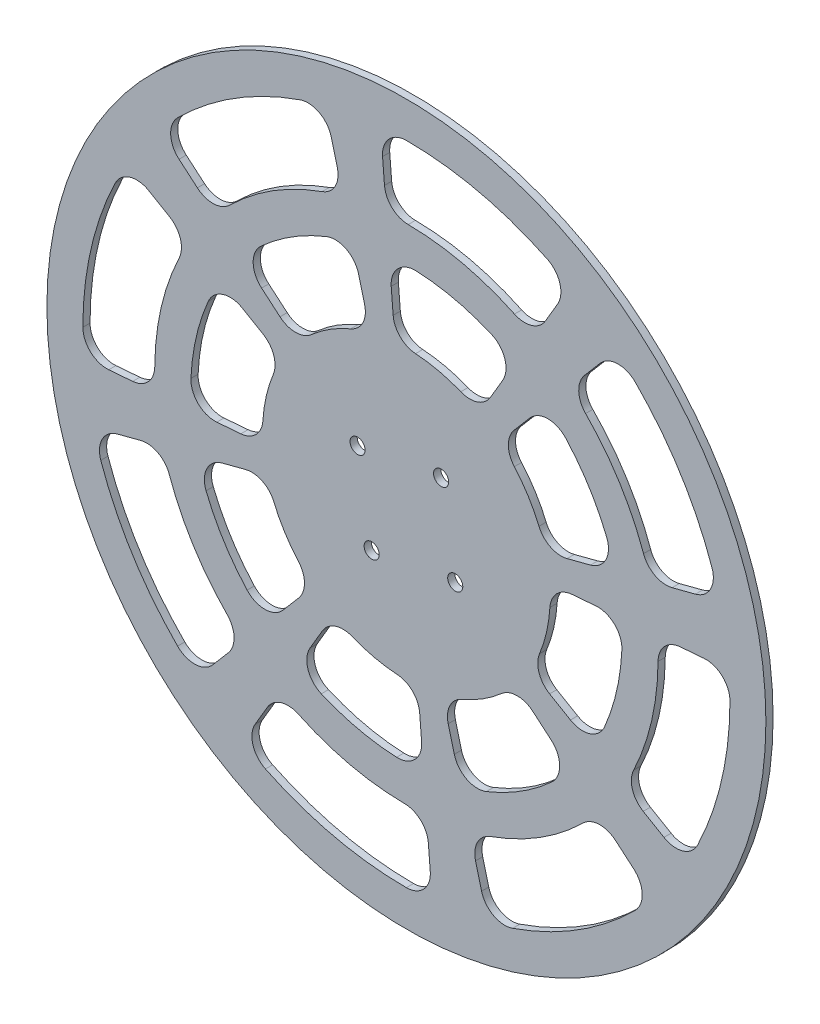
SolidWorks part; units mm, degrees
ref_plane "Front Plane" through (0, 0, 0) normal (0, 0, 1) x (1, 0, 0)
ref_plane "Top Plane" through (0, 0, 0) normal (0, 1, 0) x (1, 0, 0)
ref_plane "Right Plane" through (0, 0, 0) normal (1, 0, 0) x (0, 0, -1)
sketch "Sketch1" plane through (0, 0, 0) normal (0, 0, 1) x (1, 0, 0)
  line L0 (0, 0) -> (0, 140) construction
  line L1 (0, 140) -> (0, 150) construction
  line L2 (-12.5, 140) -> (12.5, 140) construction
  circle A0 centre (0, 0) radius 150
  circle A5 centre (20.3733, -14.4889) radius 3.15
  circle A6 centre (-14.4889, -20.3733) radius 3.15
  circle A7 centre (-20.3733, 14.4889) radius 3.15
  circle A8 centre (14.4889, 20.3733) radius 3.15
  point P9 (0, 140)
  point P21 (0, 0)
  dimension "D1" = 300
  dimension "D2" = 6.3
  dimension "D4" = 6.3
  dimension "D3" = 6.3
  dimension "D6" = 6.3
  dimension "D5" = 140
extrude "Boss-Extrude2" add sketch "Sketch1" along normal blind 3
sketch "Weight Reduction Cutouts" plane through (0, 0, 0) normal (0, 0, 1) x (1, 0, 0)
  line L3 (-33.985, 130.6523) -> (0, 0) construction
  line L4 (0, 0) -> (-102.778, 87.5311) construction
  line L5 (-94.8598, 80.7875) -> (-87.22, 74.2811)
  line L6 (-31.3667, 120.5866) -> (-28.8405, 110.8748)
  line L7 (-14.4889, -20.3733) -> (-20.3733, 14.4889) construction
  line L8 (-20.3733, 14.4889) -> (14.4889, 20.3733) construction
  line L9 (14.4889, 20.3733) -> (20.3733, -14.4889) construction
  line L10 (20.3733, -14.4889) -> (-14.4889, -20.3733) construction
  line L11 (-60.4278, 51.4634) -> (-52.7457, 44.921)
  line L12 (-19.9813, 76.8163) -> (-17.4411, 67.0508)
  line L13 (63.088, 107.4472) -> (58.007, 98.7937)
  line L14 (-9.9506, 124.2014) -> (-9.1492, 114.1985)
  line L15 (40.1884, 68.4463) -> (35.0793, 59.7448)
  line L16 (-6.3387, 79.119) -> (-5.5329, 69.0607)
  line L17 (120.5866, 31.3667) -> (110.8748, 28.8405)
  line L18 (80.7875, 94.8598) -> (74.2811, 87.22)
  line L19 (76.8163, 19.9813) -> (67.0508, 17.4411)
  line L20 (51.4634, 60.4278) -> (44.921, 52.7457)
  line L21 (107.4472, -63.088) -> (98.7937, -58.007)
  line L22 (124.2014, 9.9506) -> (114.1985, 9.1492)
  line L23 (68.4463, -40.1884) -> (59.7448, -35.0793)
  line L24 (79.119, 6.3387) -> (69.0607, 5.5329)
  line L25 (31.3667, -120.5866) -> (28.8405, -110.8748)
  line L26 (94.8598, -80.7875) -> (87.22, -74.2811)
  line L27 (19.9813, -76.8163) -> (17.4411, -67.0508)
  line L28 (60.4278, -51.4634) -> (52.7457, -44.921)
  line L29 (-63.088, -107.4472) -> (-58.007, -98.7937)
  line L30 (9.9506, -124.2014) -> (9.1492, -114.1985)
  line L31 (-40.1884, -68.4463) -> (-35.0793, -59.7448)
  line L32 (6.3387, -79.119) -> (5.5329, -69.0607)
  line L33 (-120.5866, -31.3667) -> (-110.8748, -28.8405)
  line L34 (-80.7875, -94.8598) -> (-74.2811, -87.22)
  line L35 (-76.8163, -19.9813) -> (-67.0508, -17.4411)
  line L36 (-51.4634, -60.4278) -> (-44.921, -52.7457)
  line L37 (-107.4472, 63.088) -> (-98.7937, 58.007)
  line L38 (-124.2014, -9.9506) -> (-114.1985, -9.1492)
  line L39 (-68.4463, 40.1884) -> (-59.7448, 35.0793)
  line L40 (-79.119, -6.3387) -> (-69.0607, -5.5329)
  line L41 (0, 0) -> (-25.6542, 151.9908) construction
  arc A6 (-95.4461, 95.4728) -> (-44.3283, 127.5147) centre (0, 0) cw
  arc A7 (-73.7156, 74.773) -> (-35.1691, 98.935) centre (0, 0) cw
  arc A8 (-60.687, 66.4612) -> (-33.3667, 83.5863) centre (0, 0) cw
  arc A9 (-39.6531, 45.0293) -> (-23.2449, 55.3143) centre (0, 0) cw
  arc A10 (-23.2449, 55.3143) -> (-17.4411, 67.0508) centre (-27.1191, 64.5334) ccw
  arc A11 (-39.6531, 45.0293) -> (-52.7457, 44.921) centre (-46.2619, 52.5342) cw
  arc A12 (-33.3667, 83.5863) -> (-19.9813, 76.8163) centre (-29.6593, 74.2989) cw
  arc A13 (-60.687, 66.4612) -> (-60.4278, 51.4634) centre (-53.944, 59.0766) ccw
  arc A14 (-35.1691, 98.935) -> (-28.8405, 110.8748) centre (-38.5185, 108.3574) ccw
  arc A15 (-73.7156, 74.773) -> (-87.22, 74.2811) centre (-80.7362, 81.8943) cw
  arc A16 (-44.3283, 127.5147) -> (-31.3667, 120.5866) centre (-41.0447, 118.0692) cw
  arc A17 (-95.4461, 95.4728) -> (-94.8598, 80.7875) centre (-88.376, 88.4007) ccw
  arc A18 (58.8217, 121.5113) -> (63.088, 107.4472) centre (54.4645, 112.5105) cw
  arc A19 (45.0893, 94.8259) -> (58.007, 98.7937) centre (49.3836, 103.8569) ccw
  arc A20 (0.7477, 104.9973) -> (45.0893, 94.8259) centre (0, 0) cw
  arc A21 (0.7477, 104.9973) -> (-9.1492, 114.1985) centre (0.8189, 114.9971) cw
  arc A22 (0.0189, 135) -> (-9.9506, 124.2014) centre (0.0175, 125) ccw
  arc A23 (0.0189, 135) -> (58.8217, 121.5113) centre (0, 0) cw
  arc A24 (35.5106, 82.6982) -> (40.1884, 68.4463) centre (31.565, 73.5095) cw
  arc A25 (22.6765, 55.5498) -> (35.0793, 59.7448) centre (26.4559, 64.8081) ccw
  arc A26 (3.8016, 59.8794) -> (22.6765, 55.5498) centre (0, 0) cw
  arc A27 (3.8016, 59.8794) -> (-5.5329, 69.0607) centre (4.4352, 69.8594) cw
  arc A28 (4.083, 89.9073) -> (-6.3387, 79.119) centre (3.6293, 79.9176) ccw
  arc A29 (4.083, 89.9073) -> (35.5106, 82.6982) centre (0, 0) cw
  arc A30 (127.5147, 44.3283) -> (120.5866, 31.3667) centre (118.0692, 41.0447) cw
  arc A31 (98.935, 35.1691) -> (110.8748, 28.8405) centre (108.3574, 38.5185) ccw
  arc A32 (74.773, 73.7156) -> (98.935, 35.1691) centre (0, 0) cw
  arc A33 (74.773, 73.7156) -> (74.2811, 87.22) centre (81.8943, 80.7362) cw
  arc A34 (95.4728, 95.4461) -> (80.7875, 94.8598) centre (88.4007, 88.376) ccw
  arc A35 (95.4728, 95.4461) -> (127.5147, 44.3283) centre (0, 0) cw
  arc A36 (83.5863, 33.3667) -> (76.8163, 19.9813) centre (74.2989, 29.6593) cw
  arc A37 (55.3143, 23.2449) -> (67.0508, 17.4411) centre (64.5334, 27.1191) ccw
  arc A38 (45.0293, 39.6531) -> (55.3143, 23.2449) centre (0, 0) cw
  arc A39 (45.0293, 39.6531) -> (44.921, 52.7457) centre (52.5342, 46.2619) cw
  arc A40 (66.4612, 60.687) -> (51.4634, 60.4278) centre (59.0766, 53.944) ccw
  arc A41 (66.4612, 60.687) -> (83.5863, 33.3667) centre (0, 0) cw
  arc A42 (121.5113, -58.8217) -> (107.4472, -63.088) centre (112.5105, -54.4645) cw
  arc A43 (94.8259, -45.0893) -> (98.7937, -58.007) centre (103.8569, -49.3836) ccw
  arc A44 (104.9973, -0.7477) -> (94.8259, -45.0893) centre (0, 0) cw
  arc A45 (104.9973, -0.7477) -> (114.1985, 9.1492) centre (114.9971, -0.8189) cw
  arc A46 (135, -0.0189) -> (124.2014, 9.9506) centre (125, -0.0175) ccw
  arc A47 (135, -0.0189) -> (121.5113, -58.8217) centre (0, 0) cw
  arc A48 (82.6982, -35.5106) -> (68.4463, -40.1884) centre (73.5095, -31.565) cw
  arc A49 (55.5498, -22.6765) -> (59.7448, -35.0793) centre (64.8081, -26.4559) ccw
  arc A50 (59.8794, -3.8016) -> (55.5498, -22.6765) centre (0, 0) cw
  arc A51 (59.8794, -3.8016) -> (69.0607, 5.5329) centre (69.8594, -4.4352) cw
  arc A52 (89.9073, -4.083) -> (79.119, 6.3387) centre (79.9176, -3.6293) ccw
  arc A53 (89.9073, -4.083) -> (82.6982, -35.5106) centre (0, 0) cw
  arc A54 (44.3283, -127.5147) -> (31.3667, -120.5866) centre (41.0447, -118.0692) cw
  arc A55 (35.1691, -98.935) -> (28.8405, -110.8748) centre (38.5185, -108.3574) ccw
  arc A56 (73.7156, -74.773) -> (35.1691, -98.935) centre (0, 0) cw
  arc A57 (73.7156, -74.773) -> (87.22, -74.2811) centre (80.7362, -81.8943) cw
  arc A58 (95.4461, -95.4728) -> (94.8598, -80.7875) centre (88.376, -88.4007) ccw
  arc A59 (95.4461, -95.4728) -> (44.3283, -127.5147) centre (0, 0) cw
  arc A60 (33.3667, -83.5863) -> (19.9813, -76.8163) centre (29.6593, -74.2989) cw
  arc A61 (23.2449, -55.3143) -> (17.4411, -67.0508) centre (27.1191, -64.5334) ccw
  arc A62 (39.6531, -45.0293) -> (23.2449, -55.3143) centre (0, 0) cw
  arc A63 (39.6531, -45.0293) -> (52.7457, -44.921) centre (46.2619, -52.5342) cw
  arc A64 (60.687, -66.4612) -> (60.4278, -51.4634) centre (53.944, -59.0766) ccw
  arc A65 (60.687, -66.4612) -> (33.3667, -83.5863) centre (0, 0) cw
  arc A66 (-58.8217, -121.5113) -> (-63.088, -107.4472) centre (-54.4645, -112.5105) cw
  arc A67 (-45.0893, -94.8259) -> (-58.007, -98.7937) centre (-49.3836, -103.8569) ccw
  arc A68 (-0.7477, -104.9973) -> (-45.0893, -94.8259) centre (0, 0) cw
  arc A69 (-0.7477, -104.9973) -> (9.1492, -114.1985) centre (-0.8189, -114.9971) cw
  arc A70 (-0.0189, -135) -> (9.9506, -124.2014) centre (-0.0175, -125) ccw
  arc A71 (-0.0189, -135) -> (-58.8217, -121.5113) centre (0, 0) cw
  arc A72 (-35.5106, -82.6982) -> (-40.1884, -68.4463) centre (-31.565, -73.5095) cw
  arc A73 (-22.6765, -55.5498) -> (-35.0793, -59.7448) centre (-26.4559, -64.8081) ccw
  arc A74 (-3.8016, -59.8794) -> (-22.6765, -55.5498) centre (0, 0) cw
  arc A75 (-3.8016, -59.8794) -> (5.5329, -69.0607) centre (-4.4352, -69.8594) cw
  arc A76 (-4.083, -89.9073) -> (6.3387, -79.119) centre (-3.6293, -79.9176) ccw
  arc A77 (-4.083, -89.9073) -> (-35.5106, -82.6982) centre (0, 0) cw
  arc A78 (-127.5147, -44.3283) -> (-120.5866, -31.3667) centre (-118.0692, -41.0447) cw
  arc A79 (-98.935, -35.1691) -> (-110.8748, -28.8405) centre (-108.3574, -38.5185) ccw
  arc A80 (-74.773, -73.7156) -> (-98.935, -35.1691) centre (0, 0) cw
  arc A81 (-74.773, -73.7156) -> (-74.2811, -87.22) centre (-81.8943, -80.7362) cw
  arc A82 (-95.4728, -95.4461) -> (-80.7875, -94.8598) centre (-88.4007, -88.376) ccw
  arc A83 (-95.4728, -95.4461) -> (-127.5147, -44.3283) centre (0, 0) cw
  arc A84 (-83.5863, -33.3667) -> (-76.8163, -19.9813) centre (-74.2989, -29.6593) cw
  arc A85 (-55.3143, -23.2449) -> (-67.0508, -17.4411) centre (-64.5334, -27.1191) ccw
  arc A86 (-45.0293, -39.6531) -> (-55.3143, -23.2449) centre (0, 0) cw
  arc A87 (-45.0293, -39.6531) -> (-44.921, -52.7457) centre (-52.5342, -46.2619) cw
  arc A88 (-66.4612, -60.687) -> (-51.4634, -60.4278) centre (-59.0766, -53.944) ccw
  arc A89 (-66.4612, -60.687) -> (-83.5863, -33.3667) centre (0, 0) cw
  arc A90 (-121.5113, 58.8217) -> (-107.4472, 63.088) centre (-112.5105, 54.4645) cw
  arc A91 (-94.8259, 45.0893) -> (-98.7937, 58.007) centre (-103.8569, 49.3836) ccw
  arc A92 (-104.9973, 0.7477) -> (-94.8259, 45.0893) centre (0, 0) cw
  arc A93 (-104.9973, 0.7477) -> (-114.1985, -9.1492) centre (-114.9971, 0.8189) cw
  arc A94 (-135, 0.0189) -> (-124.2014, -9.9506) centre (-125, 0.0175) ccw
  arc A95 (-135, 0.0189) -> (-121.5113, 58.8217) centre (0, 0) cw
  arc A96 (-82.6982, 35.5106) -> (-68.4463, 40.1884) centre (-73.5095, 31.565) cw
  arc A97 (-55.5498, 22.6765) -> (-59.7448, 35.0793) centre (-64.8081, 26.4559) ccw
  arc A98 (-59.8794, 3.8016) -> (-55.5498, 22.6765) centre (0, 0) cw
  arc A99 (-59.8794, 3.8016) -> (-69.0607, -5.5329) centre (-69.8594, 4.4352) cw
  arc A100 (-89.9073, 4.083) -> (-79.119, -6.3387) centre (-79.9176, 3.6293) ccw
  arc A101 (-89.9073, 4.083) -> (-82.6982, 35.5106) centre (0, 0) cw
  point P20 (-15.1045, 58.0677)
  point P23 (-45.6791, 38.9027)
  point P26 (-22.6567, 87.1015)
  point P29 (-68.5186, 58.3541)
  point P32 (-26.4328, 101.6184)
  point P35 (-79.9384, 68.0797)
  point P212 (0, 0)
  dimension "D1" = 90
  dimension "D2" = 60
  dimension "D3" = 35
  dimension "D4" = 135
  dimension "D5" = 105
  dimension "D6" = 10
  dimension "D9" = 5
  dimension "D7" = 8
extrude "Cutouts" cut sketch "Weight Reduction Cutouts" along normal through all
